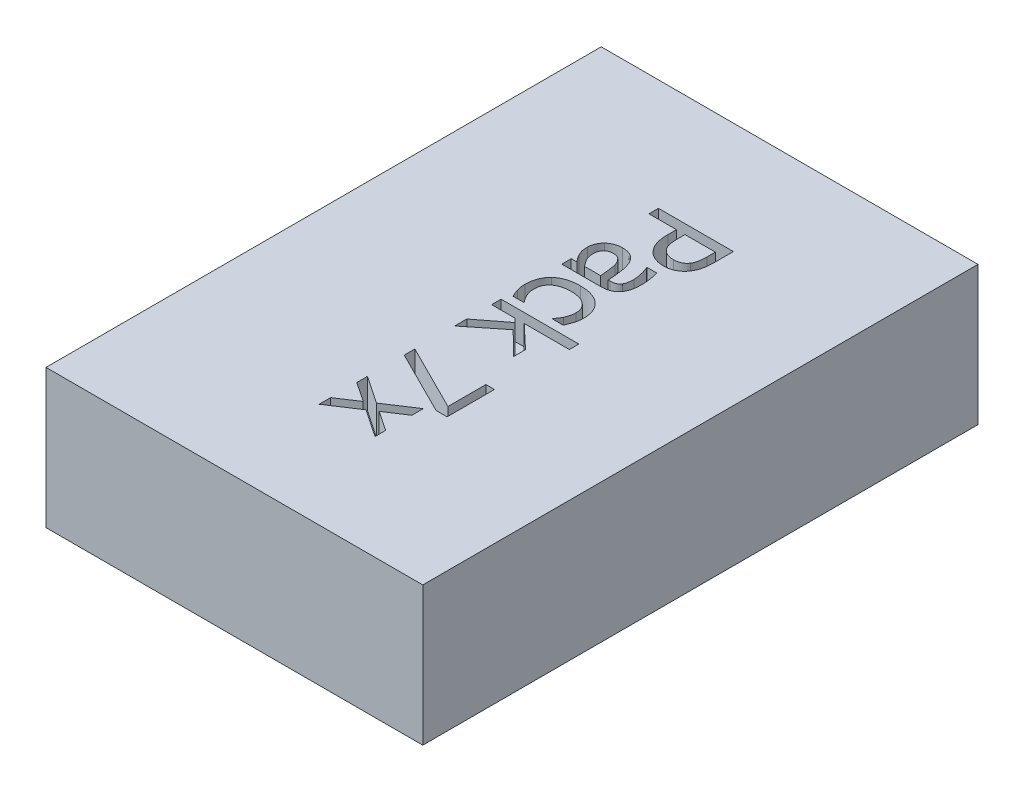
SolidWorks part; units mm, degrees
material "Rubber"
ref_plane "Спереди" through (0, 0, 0) normal (0, 0, 1) x (1, 0, 0)
ref_plane "Сверху" through (0, 0, 0) normal (0, 1, 0) x (1, 0, 0)
ref_plane "Справа" through (0, 0, 0) normal (1, 0, 0) x (0, 0, -1)
sketch "Sketch1" plane through (0, 0, 0) normal (0, 0, 1) x (1, 0, 0)
  line L1 (-19, -7) -> (19, -7)
  line L2 (-19, -7) -> (-19, 7)
  line L3 (-19, 7) -> (19, 7)
  line L4 (19, -7) -> (19, 7)
  line L5 (-19, -7) -> (19, 7) construction
  line L6 (-19, 7) -> (19, -7) construction
  point P0 (0, 0)
  dimension "D1" = 38
  dimension "D2" = 14
extrude "Boss-Extrude1" add sketch "Sketch1" along normal blind 56
sketch "Sketch2" plane through (0, 7, 0) normal (0, 1, 0) x (1, 0, 0)
  line L0 (-2.0076, 0) -> (-2.0076, -56) construction
  line L1 (19, 0) -> (-19, 0) construction
  line L2 (19, -56) -> (-19, -56) construction
  text T0 "Pack 7x" font "Tahoma" height in points 28
extrude "Cut-Extrude1" cut sketch "Sketch2" against normal blind 3
